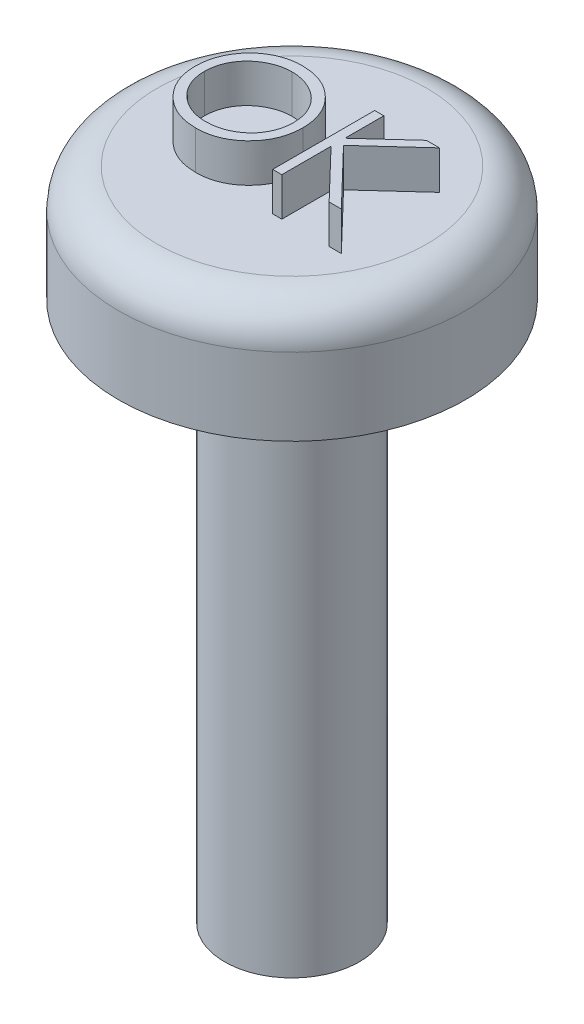
SolidWorks part; units mm, degrees
ref_plane "Front Plane" through (0, 0, 0) normal (0, 0, 1) x (1, 0, 0)
ref_plane "Top Plane" through (0, 0, 0) normal (0, 1, 0) x (1, 0, 0)
ref_plane "Right Plane" through (0, 0, 0) normal (1, 0, 0) x (0, 0, -1)
ref_plane "Plane1" through (0, 115.6015, 0) normal (0, 1, 0) x (1, 0, 0)
sketch "Sketch1" plane through (0, 115.6015, 0) normal (0, 1, 0) x (1, 0, 0)
  circle A0 centre (40.9103, -143.1552) radius 4.5
  dimension "D1" = 9
extrude "Boss-Extrude1" add sketch "Sketch1" along normal blind 3
fillet "Fillet1" radius 1 1 edges at (40.9103, 118.6015, 147.6551)
ref_plane "Plane3" through (0, 115.6015, 0) normal (0, -1, 0) x (-1, 0, 0)
sketch "Sketch6" plane through (0, 115.6015, 0) normal (0, -1, 0) x (-1, 0, 0)
  circle A0 centre (-40.9103, -143.1552) radius 4.5 construction
  circle A1 centre (-40.9103, -143.1552) radius 4.5 construction
  circle A2 centre (-40.9103, -143.1552) radius 1.75
  dimension "D1" = 3.5
extrude "Boss-Extrude3" add sketch "Sketch6" along normal blind 14
sketch "Sketch7" plane through (0, 118.6015, 0) normal (0, 1, 0) x (1, 0, 0)
  text T0 "OK" font "Century Gothic" height in points 10
extrude "Boss-Extrude4" add sketch "Sketch7" along normal blind 1
